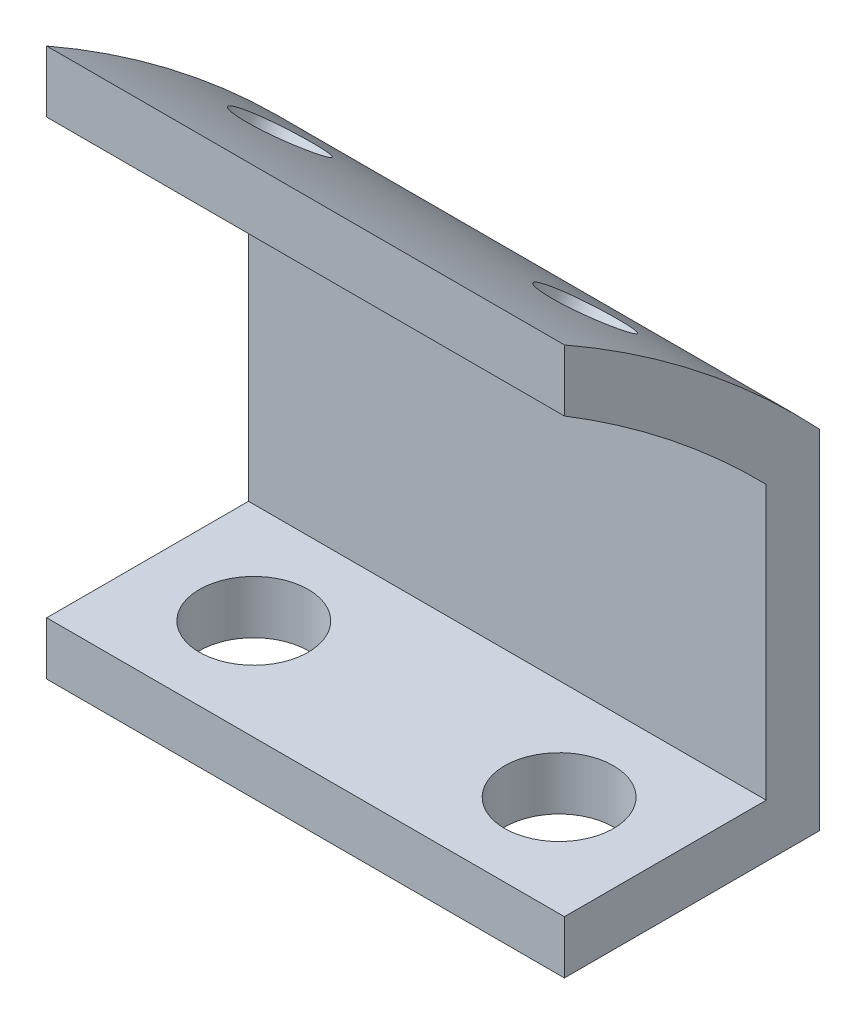
SolidWorks part; units mm, degrees
material "Alliage 1060"
ref_plane "Plan de face" through (0, 0, 0) normal (0, 0, 1) x (1, 0, 0)
ref_plane "Plan de dessus" through (0, 0, 0) normal (0, 1, 0) x (1, 0, 0)
ref_plane "Plan de droite" through (0, 0, 0) normal (1, 0, 0) x (0, 0, -1)
sketch "Esquisse1" plane through (0, 0, 0) normal (1, 0, 0) x (0, 0, -1)
  line L0 (-72.5787, 0) -> (81.4659, 0) construction
  line L1 (-72.5787, 15) -> (81.4659, 15) construction
  line L2 (0, 0) -> (0, 51.6609) construction
  line L3 (29.85, 0) -> (29.85, 51.6609) construction
  line L4 (29.85, 15) -> (29.85, 28.1065)
  line L5 (29.85, 15) -> (20.25, 15)
  line L6 (20.25, 15) -> (20.25, 17)
  line L7 (20.25, 17) -> (27.85, 17)
  line L8 (27.85, 17) -> (27.85, 27.3016)
  line L9 (20.25, 33.3307) -> (20.25, 35.6502)
  line L10 (25.0496, 32.4579) -> (34.7148, 44.9816) construction
  line L11 (0, 0) -> (39.3055, 50.93) construction
  circle A0 centre (0, 0) radius 41 construction
  arc A1 (29.85, 28.1065) -> (20.25, 35.6502) centre (0, 0) ccw
  arc A2 (27.85, 27.3016) -> (20.25, 33.3307) centre (0, 0) ccw
  dimension "D1" = 82
  dimension "D7" = 0
  dimension "D8" = 0
  dimension "D9" = 39
  dimension "D2" = 15
  dimension "D3" = 29.85
  dimension "D4" = 7.6
  dimension "D5" = 2
  dimension "D6" = 2
  dimension "D10" = 5.75
extrude "Boss.-Extru.1" add sketch "Esquisse1" along normal blind 19.5
hole_wizard "Dégagement M3.51" positions "Esquisse8" profile "Esquisse9" hole size "M3.5" standard "ISO" end condition up to next
sketch "Esquisse8" plane through (0, 15, 0) normal (0, -1, 0) x (-1, 0, 0)
  line L0 (-19.5, 20.25) -> (-19.5, 29.85) construction
  line L1 (-19.5, 20.25) -> (0, 20.25) construction
  point P0 (-15.5, 24.05)
  point P2 (-4, 24.05)
  dimension "D1" = 4
  dimension "D2" = 3.8
  dimension "D3" = 3.8
  dimension "D4" = 11.5
sketch "Esquisse9" plane through (15.5, 15, -24.05) normal (1, 0, 0) x (0, 0, -1)
  line L0 (0, 0) -> (0, 2)
  line L1 (0, 2) -> (2.05, 2)
  line L2 (2.05, 2) -> (2.05, 0)
  line L5 (2.05, 0) -> (0, 0)
  line L11 (0, -6.35) -> (0, 107.95) construction
  dimension "Diamètre du perçage jusqu'au prochain" = 4.1
  dimension "Profondeur du perçage jusqu'au prochain" = 2
hole_wizard "Dégagement M2.51" positions "Esquisse3D1" profile "Esquisse11" hole size "M2.5" standard "ISO"
sketch3d "Esquisse3D1"
  line L1 (19.5, 35.6502, -20.25) -> (0, 35.6502, -20.25) construction
  point P0 (4, 32.4667, -25.0383)
  point P2 (15.5, 32.4667, -25.0383)
  dimension "D1" = 5.75
  dimension "D2" = 5.75
  dimension "D3" = 11.5
  dimension "D4" = 4
sketch "Esquisse11" plane through (4, 32.4667, -25.0383) normal (1, 0, 0) x (0, 0.6107, 0.7919)
  line L0 (0, 0) -> (0, 2)
  line L1 (0, 2) -> (1.55, 2)
  line L2 (1.55, 2) -> (1.55, 0)
  line L5 (1.55, 0) -> (0, 0)
  line L11 (0, -6.35) -> (0, 107.95) construction
  dimension "Diamètre du perçage jusqu'au prochain" = 3.1
  dimension "Profondeur du perçage jusqu'au prochain" = 2
